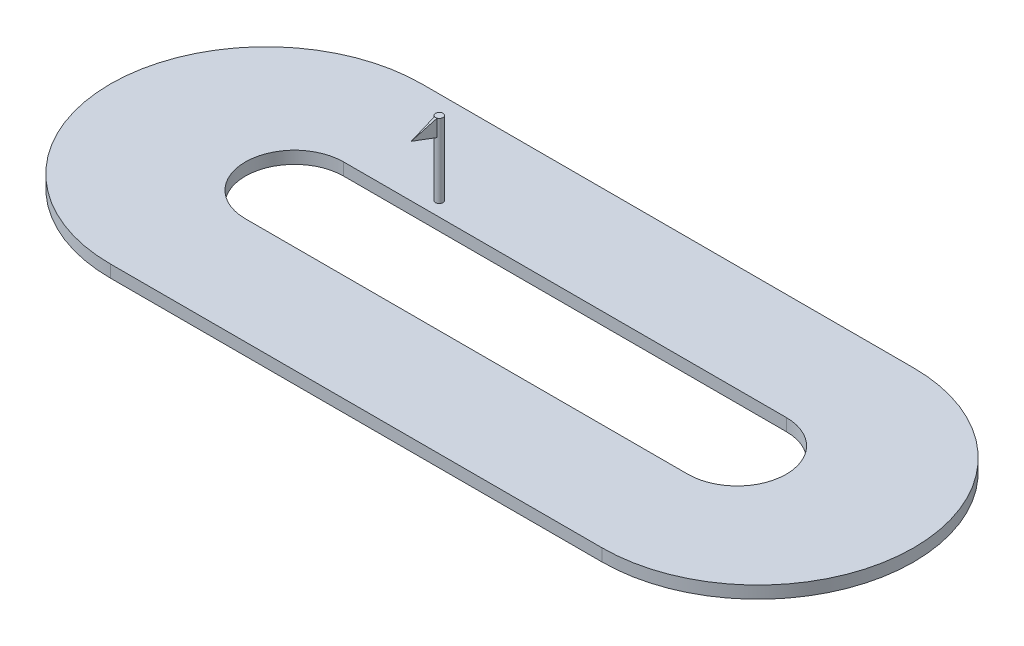
SolidWorks part; units mm, degrees
ref_plane "Front Plane" through (0, 0, 0) normal (0, 0, 1) x (1, 0, 0)
ref_plane "Top Plane" through (0, 0, 0) normal (0, 1, 0) x (1, 0, 0)
ref_plane "Right Plane" through (0, 0, 0) normal (1, 0, 0) x (0, 0, -1)
sketch "Sketch1" plane through (0, 0, 0) normal (0, 1, 0) x (1, 0, 0)
  line L4 (-6645.6009, 3345.3119) -> (13354.3991, 3345.3119)
  line L5 (-5491.5943, -991.6424) -> (12508.4057, -991.6424)
  line L6 (-5491.5943, -4991.6424) -> (12508.4057, -4991.6424)
  line L7 (-6645.6009, -9328.5967) -> (13354.3991, -9328.5967)
  arc A0 (-5491.5943, -4991.6424) -> (-5491.5943, -991.6424) centre (-5491.5943, -2991.6424) cw
  arc A1 (12508.4057, -4991.6424) -> (12508.4057, -991.6424) centre (12508.4057, -2991.6424) ccw
  arc A2 (13354.3991, 3345.3119) -> (13354.3991, -9328.5967) centre (13354.3991, -2991.6424) cw
  arc A3 (-6645.6009, 3345.3119) -> (-6645.6009, -9328.5967) centre (-6645.6009, -2991.6424) ccw
  dimension "D1" = 4000
  dimension "D2" = 12673.9086
  dimension "D3" = 18000
  dimension "D4" = 20000
extrude "Boss-Extrude1" add sketch "Sketch1" along normal blind 500
sketch "Sketch4" plane through (0, 500, 0) normal (0, 1, 0) x (1, 0, 0)
  line L0 (-3644.4792, 3345.3119) -> (-3644.4792, -991.6424) construction
  line L1 (13354.3991, 3345.3119) -> (-6645.6009, 3345.3119) construction
  line L2 (12508.4057, -991.6424) -> (-5491.5943, -991.6424) construction
  text T0 "START" font "Century Gothic" height in points 72
sketch "Sketch5" plane through (0, 500, 0) normal (0, 1, 0) x (1, 0, 0)
  circle A0 centre (-2186.3823, -408.6891) radius 150.6346
extrude "Boss-Extrude4" add sketch "Sketch5" along normal blind 3000
ref_plane "Plane1" through (0, 0, 559.3237) normal (0, 0, 1) x (1, 0, 0)
sketch "Sketch6" plane through (0, 0, 559.3237) normal (0, 0, 1) x (1, 0, 0)
  line L0 (-2035.7477, 3500) -> (-2337.0169, 3500) construction
  line L1 (-2236.4558, 3500) -> (-2132.2084, 3500)
  line L2 (-2236.4558, 3500) -> (-2236.4558, 2819.8905)
  line L3 (-2236.4558, 2819.8905) -> (-2132.2084, 2819.8905)
  line L4 (-2132.2084, 3500) -> (-2132.2084, 2819.8905)
extrude "Boss-Extrude5" add sketch "Sketch6" along normal blind 1000 draft 3 separate body
ref_plane "Plane2" through (-2035.7477, 0, 0) normal (1, 0, 0) x (0, 0, -1)
sketch "Sketch8" plane through (-2035.7477, 0, 0) normal (1, 0, 0) x (0, 0, -1)
  line L0 (-559.3237, 3500) -> (-559.3237, 2819.8905)
  line L1 (-559.3237, 2819.8905) -> (-1553.903, 3159.9452)
  line L2 (-1553.903, 2872.0142) -> (-1553.903, 3447.8763) construction
  line L3 (-1553.903, 3159.9452) -> (-559.3237, 3500)
  line L4 (-559.3237, 3500) -> (-1553.903, 3447.8763)
  line L5 (-1553.903, 3447.8763) -> (-1553.903, 3159.9452)
  line L6 (-559.3237, 2819.8905) -> (-1553.903, 2872.0142)
  line L7 (-1553.903, 2872.0142) -> (-1553.903, 3159.9452)
extrude "Cut-Extrude1" cut sketch "Sketch8" against normal blind 1000 contours L4 L5 L3 | L7 L6 L1
sketch "Sketch9" plane through (0, 0, 559.3237) normal (0, 0, -1) x (-1, 0, 0)
  line L4 (2236.4558, 2819.8905) -> (2236.4558, 3500)
  line L5 (2236.4558, 3500) -> (2132.2084, 3500)
  line L6 (2132.2084, 3500) -> (2132.2084, 2819.8905)
  line L7 (2132.2084, 2819.8905) -> (2236.4558, 2819.8905)
  line L8 (2236.4558, 2819.8905) -> (2236.4558, 3500)
  line L9 (2236.4558, 3500) -> (2132.2084, 3500)
  line L10 (2132.2084, 3500) -> (2132.2084, 2819.8905)
  line L11 (2132.2084, 2819.8905) -> (2236.4558, 2819.8905)
  dimension "D1" = 0
extrude "Boss-Extrude6" add sketch "Sketch9" along normal blind 50
